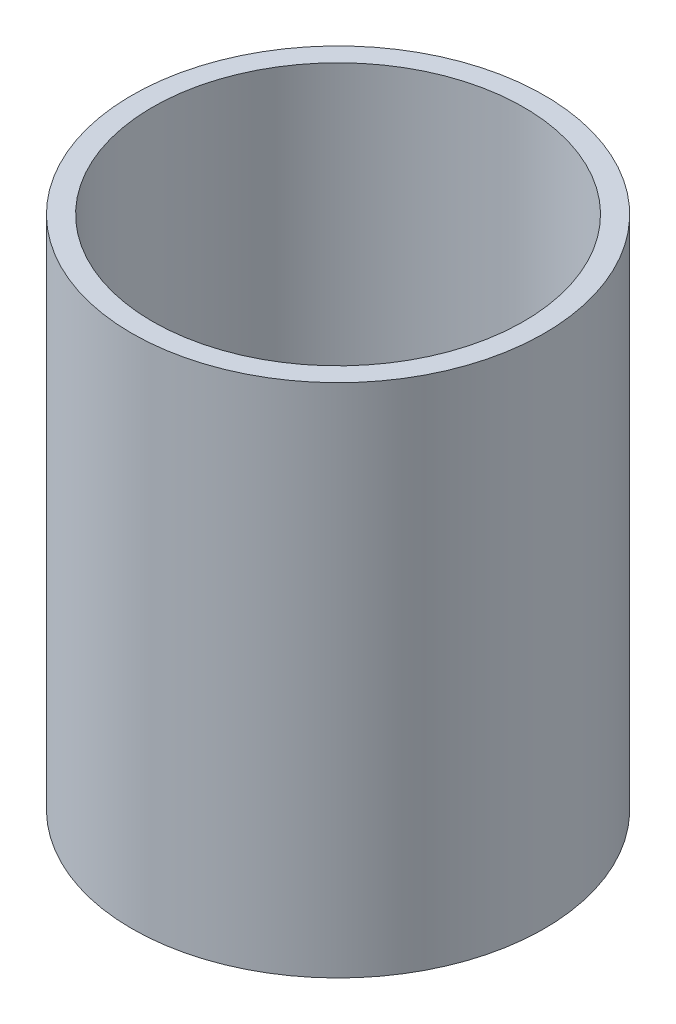
SolidWorks part; units mm, degrees
ref_plane "Front Plane" through (0, 0, 0) normal (0, 0, 1) x (1, 0, 0)
ref_plane "Top Plane" through (0, 0, 0) normal (0, 1, 0) x (1, 0, 0)
ref_plane "Right Plane" through (0, 0, 0) normal (1, 0, 0) x (0, 0, -1)
sketch "Sketch1" plane through (0, 0, 0) normal (0, 1, 0) x (1, 0, 0)
  circle A0 centre (0, 0) radius 20
  dimension "D1" = 40
extrude "Boss-Extrude1" add sketch "Sketch1" along normal blind 50
shell "Shell3" thickness 2
sketch "Sketch2" plane through (0, 2, 0) normal (0, 1, 0) x (1, 0, 0)
  line L0 (0, 18) -> (0, -18) construction
  line L1 (-1, 0) -> (1, 0) construction
  line L2 (-1, 16.9706) -> (-1, -16.9706)
  line L3 (1, 16.9706) -> (1, -16.9706)
  circle A0 centre (0, 0) radius 18 construction
  circle A1 centre (0, 0) radius 18 construction
  circle A2 centre (0, 0) radius 18
  circle A3 centre (0, 0) radius 17
  point P14 (0, 0)
  dimension "D1" = 36
  dimension "D2" = 34
  dimension "D3" = 1
extrude "Cut-Extrude1" cut sketch "Sketch2" against normal blind 50 contours L2 A3 | L3 A3
